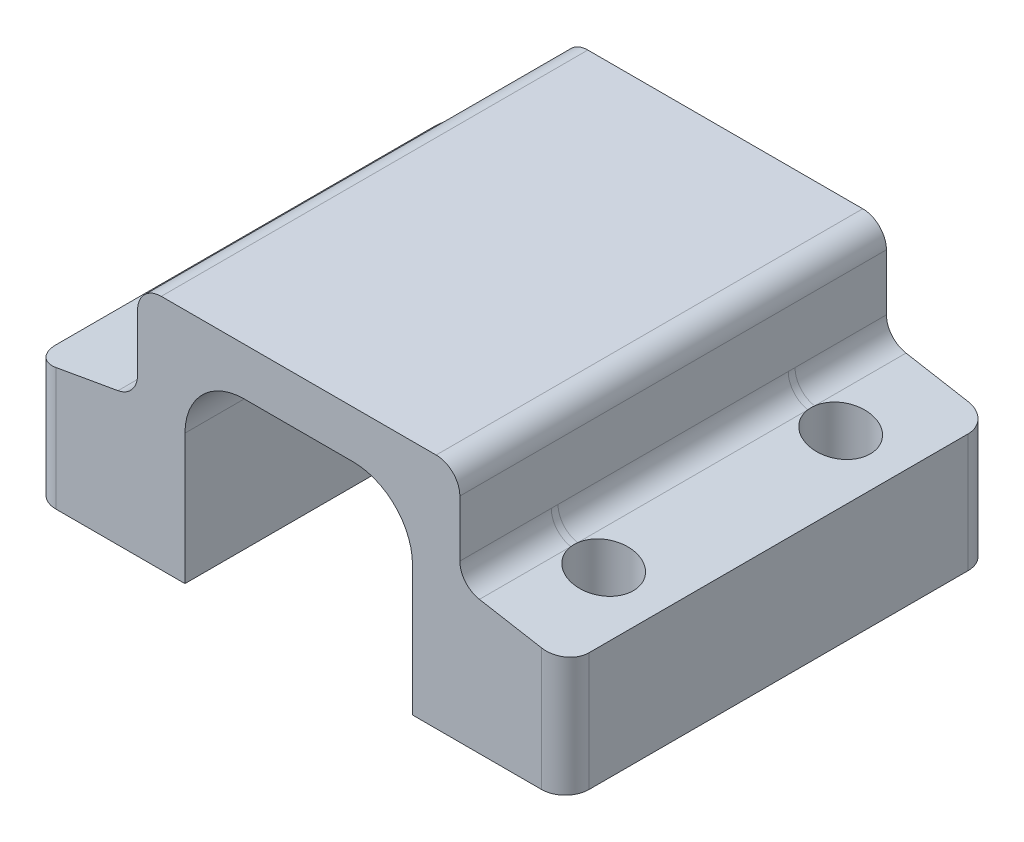
SolidWorks part; units mm, degrees
ref_plane "Front Plane" through (0, 0, 0) normal (0, 0, 1) x (1, 0, 0)
ref_plane "Top Plane" through (0, 0, 0) normal (0, 1, 0) x (1, 0, 0)
ref_plane "Right Plane" through (0, 0, 0) normal (1, 0, 0) x (0, 0, -1)
sketch "Sketch1" plane through (0, 0, 0) normal (0, 0, 1) x (1, 0, 0)
  line L0 (-92.6582, 0) -> (89.2369, 0) construction
  line L2 (-6.096, 10.16) -> (6.096, 10.16)
  line L3 (6.096, 10.16) -> (6.096, 0)
  line L4 (-6.096, 0) -> (6.096, 0) construction
  line L5 (8.89, 6.35) -> (14.2875, 6.35) construction
  line L6 (14.2875, 6.35) -> (14.2875, 0)
  line L7 (14.2875, 0) -> (6.096, 0)
  line L8 (8.636, 7.3465) -> (8.636, 12.7)
  line L9 (8.636, 12.7) -> (-8.636, 12.7)
  line L10 (0, 0) -> (0, 31.7739) construction
  line L13 (-8.636, 7.3465) -> (-8.636, 12.7)
  line L14 (-8.89, 6.35) -> (-14.2875, 6.35) construction
  line L15 (-14.2875, 6.35) -> (-14.2875, 0)
  line L16 (-14.2875, 0) -> (-6.096, 0)
  line L17 (-6.096, 10.16) -> (-6.096, 0)
  line L18 (14.2875, 6.35) -> (8.636, 7.3465)
  line L19 (-14.2875, 6.35) -> (-8.636, 7.3465)
  point P5 (0, 0)
  point P16 (0, 12.7)
  point P24 (0, 10.16)
  dimension "D1" = 10.16
  dimension "D2" = 2.54
  dimension "D3" = 12.192
  dimension "D4" = 12.7
  dimension "D5" = 6.35
  dimension "D7" = 28.575
  dimension "D8" = 10
  dimension "D9" = 10
extrude "Boss-Extrude1" add sketch "Sketch1" against normal blind 22.86
sketch "Sketch2" plane through (0, 0, 0) normal (0, 0, 1) x (1, 0, 0)
  line L0 (6.096, 10.16) -> (6.096, 0) construction
  line L1 (-6.096, 10.16) -> (6.096, 10.16) construction
  line L2 (6.096, 6.985) -> (6.096, 0) construction
  line L3 (-6.096, 10.16) -> (2.921, 10.16) construction
  line L4 (2.921, 10.16) -> (6.096, 10.16)
  line L5 (6.096, 10.16) -> (6.096, 6.985)
  line L6 (0, 0) -> (0, 17.4905) construction
  line L7 (-6.096, 10.16) -> (-6.096, 6.985)
  line L8 (-2.921, 10.16) -> (-6.096, 10.16)
  arc A0 (6.096, 6.985) -> (2.921, 10.16) centre (2.921, 6.985) ccw
  arc A1 (-6.096, 6.985) -> (-2.921, 10.16) centre (-2.921, 6.985) cw
  dimension "D1" = 3.175
extrude "Boss-Extrude2" add sketch "Sketch2" against normal blind 13.462
sketch "Sketch3" plane through (0, 0, -13.462) normal (0, 0, 1) x (1, 0, 0)
  line L2 (-6.096, 10.16) -> (-6.096, 6.985)
  line L3 (-2.921, 10.16) -> (-6.096, 10.16)
  line L4 (-6.096, 10.16) -> (-6.096, 6.985)
  line L5 (-2.921, 10.16) -> (-6.096, 10.16)
  line L6 (6.096, 10.16) -> (2.921, 10.16)
  line L7 (6.096, 6.985) -> (6.096, 10.16)
  line L8 (6.096, 10.16) -> (2.921, 10.16) construction
  line L9 (6.096, 6.985) -> (6.096, 10.16) construction
  arc A1 (-2.921, 10.16) -> (-6.096, 6.985) centre (-2.921, 6.985) ccw
  arc A2 (-2.921, 10.16) -> (-6.096, 6.985) centre (-2.921, 6.985) ccw
  arc A3 (6.096, 6.985) -> (2.921, 10.16) centre (2.921, 6.985) ccw
  arc A4 (6.096, 6.985) -> (2.921, 10.16) centre (2.921, 6.985) ccw construction
  dimension "D1" = 0
  dimension "D2" = 0
extrude "Boss-Extrude3" add sketch "Sketch3" against normal blind 1.905 from offset 1.27 offset against normal yes
sketch "Sketch4" plane through (0, 0, -16.637) normal (0, 0, 1) x (1, 0, 0)
  line L2 (-6.096, 10.16) -> (-6.096, 6.985)
  line L3 (-2.921, 10.16) -> (-6.096, 10.16)
  line L4 (-6.096, 10.16) -> (-6.096, 6.985)
  line L5 (-2.921, 10.16) -> (-6.096, 10.16)
  arc A1 (-2.921, 10.16) -> (-6.096, 6.985) centre (-2.921, 6.985) ccw
  arc A2 (-2.921, 10.16) -> (-6.096, 6.985) centre (-2.921, 6.985) ccw
  dimension "D1" = 0
extrude "Boss-Extrude4" add sketch "Sketch4" against normal blind 3.81 from offset 1.27 offset against normal yes
sketch "Sketch5" plane through (0, 0, 0) normal (0, 1, 0) x (1, 0, 0)
  line L0 (-5.9055, 22.0472) -> (5.9055, 22.0472)
  line L1 (5.9055, 22.0472) -> (5.9055, 22.86)
  line L2 (5.9055, 22.86) -> (-5.9055, 22.86)
  line L3 (-5.9055, 22.86) -> (-5.9055, 22.0472)
  line L5 (-5.9055, 17.018) -> (5.9055, 17.018)
  line L6 (-5.9055, 17.018) -> (-5.9055, 17.8308)
  line L7 (-5.9055, 17.8308) -> (5.9055, 17.8308)
  line L8 (5.9055, 17.018) -> (5.9055, 17.8308)
  line L9 (-5.9055, 13.8176) -> (5.9055, 13.8176)
  line L10 (-5.9055, 13.8176) -> (-5.9055, 14.6304)
  line L11 (-5.9055, 14.6304) -> (5.9055, 14.6304)
  line L12 (5.9055, 13.8176) -> (5.9055, 14.6304)
  line L13 (-5.9055, 13.8176) -> (5.9055, 13.8176)
  line L14 (-5.9055, 13.8176) -> (-5.9055, -1.27)
  line L15 (-5.9055, -1.27) -> (5.9055, -1.27)
  line L16 (5.9055, 13.8176) -> (5.9055, -1.27)
  line L17 (-6.096, 22.86) -> (6.096, 22.86) construction
  point P12 (0, 22.0472)
  dimension "D1" = 0.8128
  dimension "D2" = 11.811
  dimension "D3" = 5.842
  dimension "D4" = 4.0132
  dimension "D5" = 24.13
ref_plane "Plane1" through (0, 0, -5.08) normal (0, 0, 1) x (1, 0, 0)
sketch "Sketch6" plane through (0, 0, -5.08) normal (0, 0, 1) x (1, 0, 0)
  line L0 (13.889, 6.4203) -> (8.636, 7.3465) construction
  line L1 (8.636, 7.3465) -> (9.0771, 9.8479) construction
  line L2 (9.0771, 9.8479) -> (14.33, 8.9217) construction
  line L3 (14.33, 8.9217) -> (13.889, 6.4203) construction
  line L4 (11.2625, 6.8834) -> (11.2625, -1.27) construction
  line L5 (6.096, 0) -> (14.2875, 0) construction
  line L6 (8.636, 7.3465) -> (8.636, 12.7) construction
  line L8 (11.2625, -1.27) -> (12.85, -1.27)
  line L9 (12.85, -1.27) -> (12.85, 6.6035)
  line L10 (12.85, 6.6035) -> (11.2625, 6.8834) construction
  line L11 (11.2625, 6.8834) -> (11.2625, -1.27)
  line L12 (11.2625, -1.27) -> (11.2625, -5.0048) construction
  line L13 (8.636, 7.3465) -> (8.636, 6.35) construction
  line L14 (8.636, 6.35) -> (14.2875, 6.35) construction
  line L15 (14.2875, 6.35) -> (8.636, 7.3465) construction
  line L16 (12.85, 9.4234) -> (12.85, 6.6035)
  line L17 (11.2625, 6.8834) -> (11.2625, 9.4234)
  line L18 (11.2625, 9.4234) -> (12.85, 9.4234)
  dimension "D1" = 5.334
  dimension "D2" = 10
  dimension "D3" = 2.54
  dimension "D4" = 3.175
  dimension "D5" = 1.27
  dimension "D6" = 2.54
revolve "Cut-Revolve1" cut sketch "Sketch6" angle 360 about L12
mirror "Mirror1" about plane through (0, 0, 0) normal (1, 0, 0) of "Cut-Revolve1"
ref_plane "Plane2" through (0, 0, -11.43) normal (0, 0, 1) x (1, 0, 0)
mirror "Mirror2" about plane through (0, 0, -11.43) normal (0, 0, 1) of "Mirror1", "Cut-Revolve1"
fillet "Fillet1" radius 1.27 8 edges at (-8.636, 12.7, -11.43) (8.636, 12.7, -11.43) (-14.2875, 3.175, -22.86) (-14.2875, 3.175, 0) (14.2875, 3.175, -22.86) (14.2875, 3.175, 0) (-8.636, 7.3465, -11.43) (8.636, 7.3465, -11.43)
